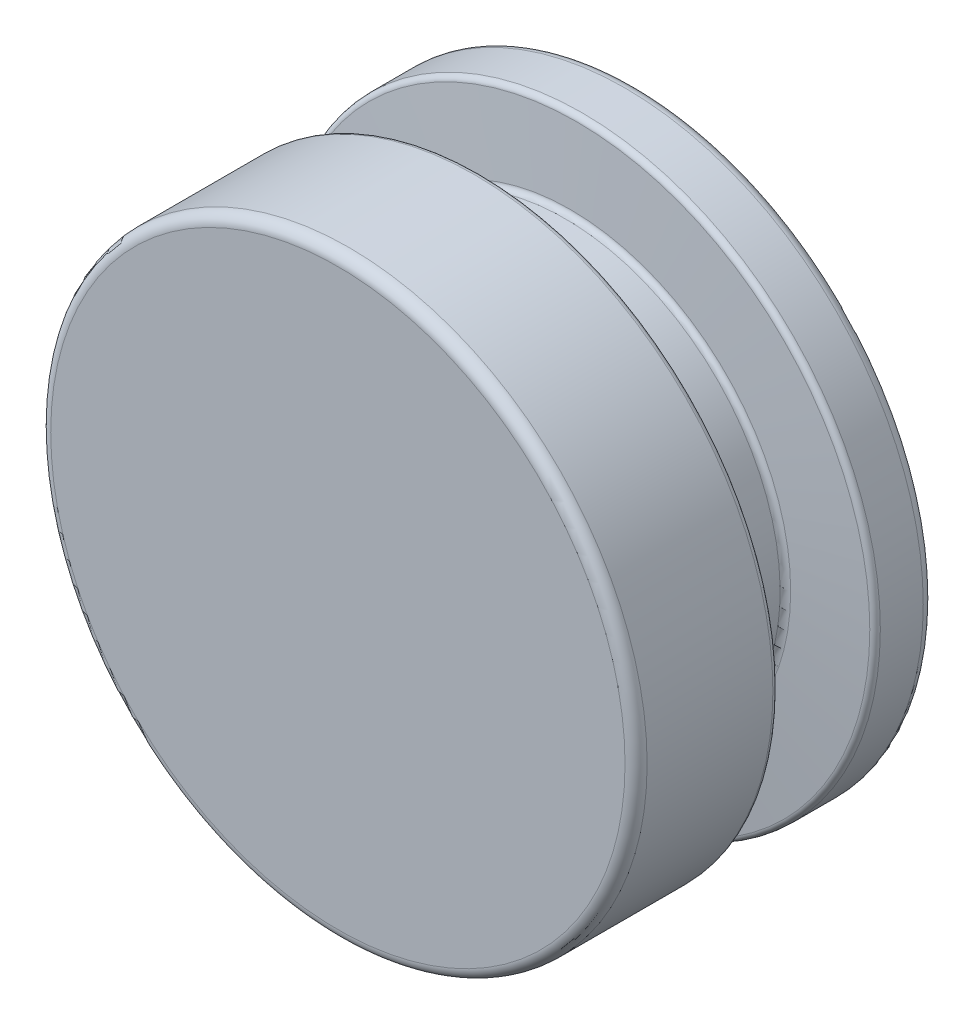
SolidWorks part; units mm, degrees
material "ABS"
ref_plane "Front Plane" through (0, 0, 0) normal (0, 0, 1) x (1, 0, 0)
ref_plane "Top Plane" through (0, 0, 0) normal (0, 1, 0) x (1, 0, 0)
ref_plane "Right Plane" through (0, 0, 0) normal (1, 0, 0) x (0, 0, -1)
sketch "Sketch1" plane through (0, 0, 0) normal (0, 0, 1) x (1, 0, 0)
  circle A3 centre (0, 0) radius 68.5736
  dimension "D2" = 137.1473
extrude "Boss-Extrude1" add sketch "Sketch1" along normal offset from surface 3.81 and the other way blind 50.8
sketch "Sketch2" plane through (0, 0, 0) normal (1, 0, 0) x (0, 0, -1)
  line L0 (-17.78, 0) -> (50.8, 0) construction
  line L1 (-17.78, 68.5736) -> (-17.78, -68.5736) construction
  line L2 (50.8, -68.5736) -> (50.8, 68.5736) construction
  line L3 (16.51, 68.5736) -> (16.51, -68.5736) construction
  line L6 (26.035, 68.5737) -> (26.035, 49.5237) construction
  line L7 (16.51, 49.5237) -> (35.56, 49.5237)
  line L8 (16.51, 49.5237) -> (14.8433, 68.5736)
  line L9 (14.8433, 68.5736) -> (37.2267, 68.5737)
  line L10 (35.56, 49.5237) -> (37.2267, 68.5737)
  line L11 (50.8, 68.5736) -> (-17.78, 68.5736) construction
  line L12 (-17.78, -68.5736) -> (50.8, -68.5736) construction
  point P17 (26.035, 68.5737)
  dimension "D1" = 95
  dimension "D2" = 19.05
  dimension "D3" = 19.05
revolve "Cut-Revolve1" cut sketch "Sketch2" angle 360 about L0
fillet "Fillet1" radius 1.27 4 edges at (0, -68.5737, -37.2267) (0, -68.5737, -14.8433) (0, -49.5237, -16.51) (0, -49.5237, -35.56)
fillet "Fillet2" radius 2.54 2 edges at (68.5736, 0, -50.8) (68.5736, 0, 17.78)
